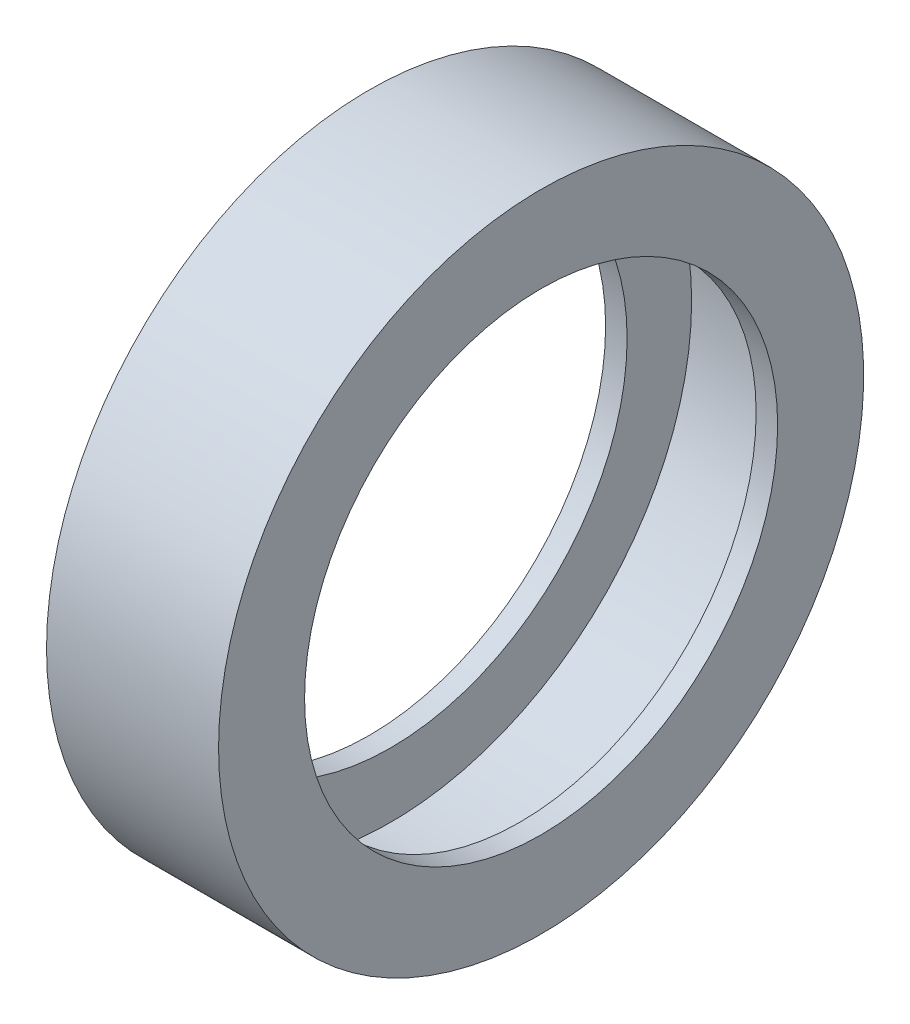
SolidWorks part; units mm, degrees
ref_plane "前基準面" through (0, 0, 0) normal (0, 0, 1) x (1, 0, 0)
ref_plane "上基準面" through (0, 0, 0) normal (0, 1, 0) x (1, 0, 0)
ref_plane "右基準面" through (0, 0, 0) normal (1, 0, 0) x (0, 0, -1)
sketch "草圖1" plane through (0, 0, 0) normal (0, 0, 1) x (1, 0, 0)
  line L0 (-91.9701, 0) -> (95.0332, 0) construction
  line L1 (55, 0) -> (-55, 0) construction
  line L2 (0, -55) -> (0, 55) construction
  line L3 (-20, 75) -> (20, 75)
  line L4 (-20, 75) -> (-20, 55)
  line L5 (-20, 55) -> (20, 55)
  line L6 (20, 75) -> (20, 55)
  line L7 (-20, 75) -> (20, 55) construction
  line L8 (-20, 55) -> (20, 75) construction
  line L10 (-15, 70) -> (15, 70)
  line L11 (-15, 70) -> (-15, 55)
  line L12 (-15, 55) -> (15, 55)
  line L13 (15, 70) -> (15, 55)
  line L14 (-15, 70) -> (15, 55) construction
  line L15 (-15, 55) -> (15, 70) construction
  point P5 (0, 65)
  point P12 (0, 45.7957)
  point P13 (0, 46.1565)
  point P14 (0, 62.5)
  dimension "D1" = 20
  dimension "D2" = 150
  dimension "D3" = 40
  dimension "D4" = 5
  dimension "D5" = 5
revolve "旋轉1" add sketch "草圖1" angle 360 about L0
equation "\"D\"=3"
